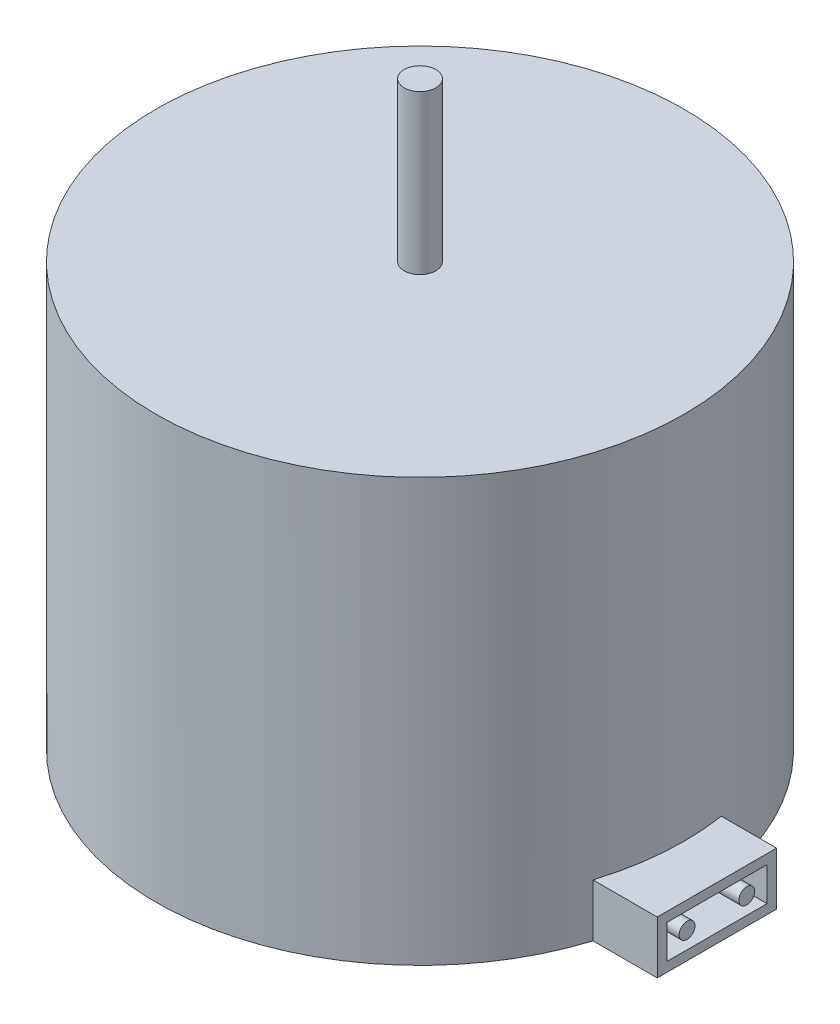
SolidWorks part; units mm, degrees
ref_plane "Front Plane" through (0, 0, 0) normal (0, 0, 1) x (1, 0, 0)
ref_plane "Top Plane" through (0, 0, 0) normal (0, 1, 0) x (1, 0, 0)
ref_plane "Right Plane" through (0, 0, 0) normal (1, 0, 0) x (0, 0, -1)
sketch "Sketch1" plane through (0, 0, 0) normal (0, 1, 0) x (1, 0, 0)
  circle A0 centre (0, 0) radius 25
extrude "Boss-Extrude1" add sketch "Sketch1" along normal blind 40
sketch "Sketch2" plane through (0, 40, 0) normal (0, 1, 0) x (1, 0, 0)
  circle A0 centre (0, 0) radius 1.5
extrude "Boss-Extrude2" add sketch "Sketch2" along normal blind 15
sketch "Sketch3" plane through (0, 0, 0) normal (0, -1, 0) x (1, 0, 0)
  line L1 (19.9326, -3.8123) -> (29.9326, -3.8123)
  line L2 (19.9326, -3.8123) -> (19.9326, 7.4801)
  line L3 (19.9326, 7.4801) -> (29.9326, 7.4801)
  line L4 (29.9326, -3.8123) -> (29.9326, 7.4801)
  line L5 (19.9326, -3.8123) -> (29.9326, 7.4801) construction
  line L6 (19.9326, 7.4801) -> (29.9326, -3.8123) construction
  circle A0 centre (0, 0) radius 25 construction
  point P0 (24.9326, 1.8339)
  dimension "D1" = 10
extrude "Boss-Extrude3" add sketch "Sketch3" against normal blind 5
sketch "Sketch4" plane through (29.9326, 0, 0) normal (1, 0, 0) x (0, 0, -1)
  line L0 (-1.8339, 0) -> (-1.8339, 5) construction
  line L1 (3.8123, 0) -> (-7.4801, 0) construction
  line L2 (3.8123, 5) -> (-7.4801, 5) construction
  line L14 (-6.5801, 0.9) -> (2.9123, 0.9)
  line L15 (2.9123, 0.9) -> (2.9123, 4.1)
  line L16 (2.9123, 4.1) -> (-6.5801, 4.1)
  line L17 (-6.5801, 4.1) -> (-6.5801, 0.9)
  line L18 (-6.5801, 0.9) -> (2.9123, 0.9)
  line L19 (2.9123, 0.9) -> (2.9123, 4.1)
  line L20 (2.9123, 4.1) -> (-6.5801, 4.1)
  line L21 (-6.5801, 4.1) -> (-6.5801, 0.9)
  circle A0 centre (-4.657, 2.5) radius 0.75
  circle A1 centre (0.9892, 2.5) radius 0.75
  dimension "D2" = 1.5
  dimension "D1" = 0.9
extrude "Cut-Extrude1" cut sketch "Sketch4" against normal blind 4 contours L18 L19 L20 L21 | A0 | A1
